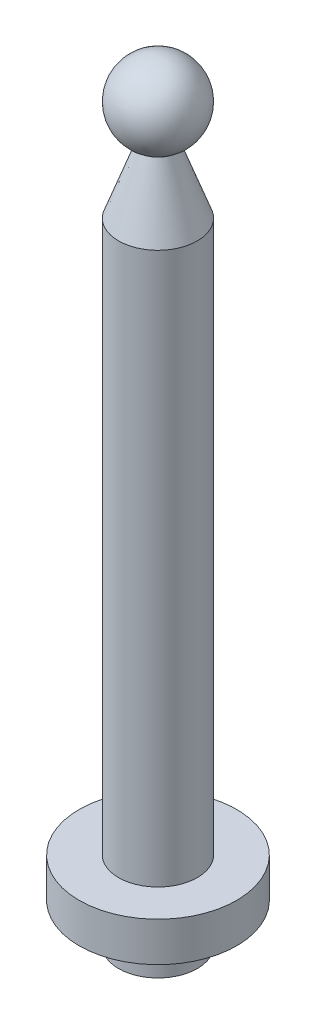
SolidWorks part; units mm, degrees
ref_plane "Front Plane" through (0, 0, 0) normal (0, 0, 1) x (1, 0, 0)
ref_plane "Top Plane" through (0, 0, 0) normal (0, 1, 0) x (1, 0, 0)
ref_plane "Right Plane" through (0, 0, 0) normal (1, 0, 0) x (0, 0, -1)
sketch "Sketch1" plane through (0, 0, 0) normal (0, 1, 0) x (1, 0, 0)
  circle A0 centre (0, 0) radius 5
  dimension "D1" = 10
extrude "Boss-Extrude1" add sketch "Sketch1" along normal blind 5
sketch "Sketch2" plane through (0, 5, 0) normal (0, 1, 0) x (1, 0, 0)
  circle A0 centre (0, 0) radius 10
  dimension "D1" = 20
extrude "Boss-Extrude2" add sketch "Sketch2" along normal blind 5
sketch "Sketch3" plane through (0, 10, 0) normal (0, 1, 0) x (1, 0, 0)
  circle A0 centre (0, 0) radius 5
  dimension "D1" = 10
extrude "Boss-Extrude3" add sketch "Sketch3" along normal blind 70
sketch "Sketch4" plane through (0, 0, 0) normal (1, 0, 0) x (0, 0, -1)
  line L0 (5, 80) -> (2, 88.2424)
  line L1 (0, 97.825) -> (0, 80)
  line L2 (0, 80) -> (5, 80)
  line L3 (5, 80) -> (-5, 80) construction
  line L4 (0, 97.825) -> (-25.7809, 97.825) construction
  arc A0 (2, 88.2424) -> (0, 97.825) centre (0, 92.825) ccw
  dimension "D3" = 5
  dimension "D1" = 70
  dimension "D2" = 2
revolve "Revolve1" add sketch "Sketch4" angle 360 about L1
